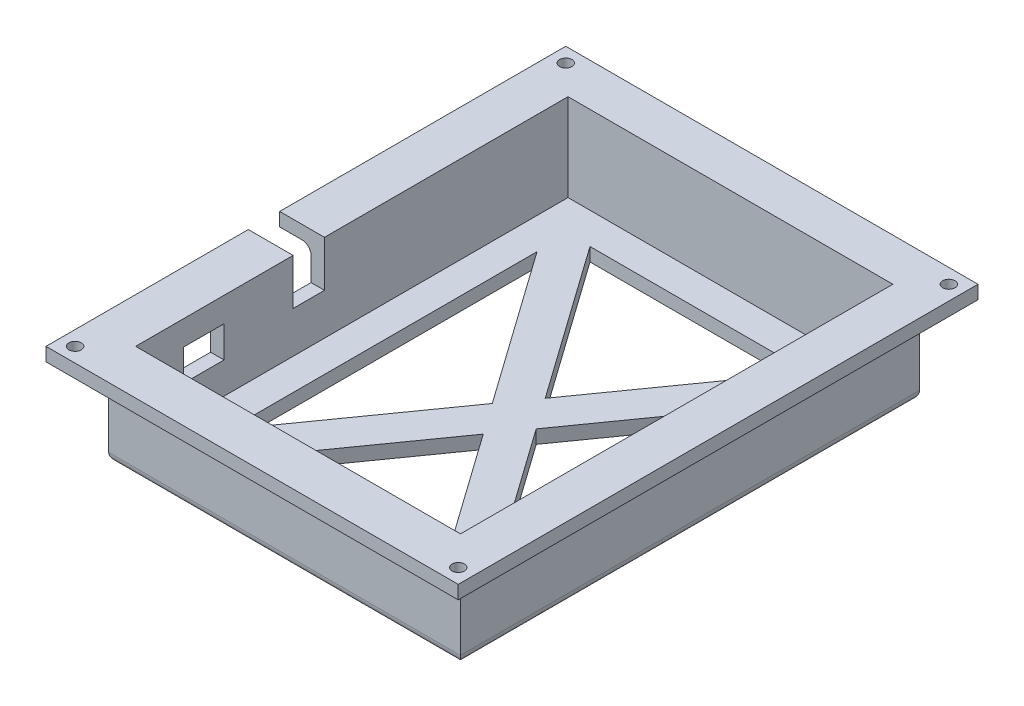
SolidWorks part; units mm, degrees
ref_plane "Front" through (0, 0, 0) normal (0, 0, 1) x (1, 0, 0)
ref_plane "Top" through (0, 0, 0) normal (0, 1, 0) x (1, 0, 0)
ref_plane "Right" through (0, 0, 0) normal (1, 0, 0) x (0, 0, -1)
sketch "Sketch1" plane through (0, 0, 0) normal (0, 1, 0) x (1, 0, 0)
  line L1 (0, 0) -> (72.5, 0)
  line L2 (0, 0) -> (0, 96.5)
  line L3 (0, 96.5) -> (72.5, 96.5)
  line L4 (72.5, 0) -> (72.5, 96.5)
  dimension "D1" = 96.5
  dimension "D2" = 72.5
extrude "bracketBase" add sketch "Sketch1" along normal blind 3
sketch "Sketch3" plane through (0, 0, 0) normal (0, -1, 0) x (1, 0, 0)
  line L0 (-3, 3) -> (-3, -99.5)
  line L1 (-3, -99.5) -> (75.5, -99.5)
  line L2 (75.5, -99.5) -> (75.5, 3)
  line L3 (75.5, 3) -> (-3, 3)
  line L4 (0, 0) -> (0, -96.5)
  line L5 (0, -96.5) -> (72.5, -96.5)
  line L6 (72.5, -96.5) -> (72.5, 0)
  line L7 (72.5, 0) -> (0, 0)
  line L8 (0, 0) -> (0, -96.5)
  line L9 (0, -96.5) -> (72.5, -96.5)
  line L10 (72.5, -96.5) -> (72.5, 0)
  line L11 (72.5, 0) -> (0, 0)
  dimension "D1" = 0
  dimension "D2" = 3
extrude "bracketWalls" add sketch "Sketch3" against normal blind 22.5
sketch "Sketch4" plane through (72.5, 0, 0) normal (-1, 0, 0) x (0, 0, 1)
  line L0 (0, 3) -> (-96.5, 3) construction
  line L1 (-42.15, 3) -> (-35.15, 3)
  line L2 (-42.15, 3) -> (-42.15, 22.5)
  line L3 (-42.15, 22.5) -> (-35.15, 22.5)
  line L4 (-35.15, 3) -> (-35.15, 22.5)
  line L5 (-96.5, 22.5) -> (0, 22.5) construction
  line L6 (0, 22.5) -> (0, 3) construction
  dimension "D1" = 42.15
  dimension "D2" = 7
extrude "wireHole" cut sketch "Sketch4" against normal blind 22.5
sketch "Sketch6" plane through (0, 22.5, 0) normal (0, 1, 0) x (1, 0, 0)
  line L12 (72.5, 96.5) -> (72.5, 42.15)
  line L13 (72.5, 42.15) -> (75.5, 42.15)
  line L14 (75.5, 42.15) -> (75.5, 99.5)
  line L15 (75.5, 99.5) -> (-3, 99.5)
  line L16 (-3, 99.5) -> (-3, -3)
  line L17 (-3, -3) -> (75.5, -3)
  line L18 (75.5, -3) -> (75.5, 35.15)
  line L19 (75.5, 35.15) -> (72.5, 35.15)
  line L20 (72.5, 35.15) -> (72.5, 0)
  line L21 (72.5, 0) -> (0, 0)
  line L22 (0, 0) -> (0, 96.5)
  line L23 (0, 96.5) -> (72.5, 96.5)
  line L24 (72.5, 96.5) -> (72.5, 42.15)
  line L32 (72.5, 35.15) -> (72.5, 0)
  line L33 (72.5, 0) -> (0, 0)
  line L34 (0, 0) -> (0, 96.5)
  line L35 (0, 96.5) -> (72.5, 96.5)
  line L48 (82, 42.15) -> (82, 106)
  line L49 (82, 106) -> (-10, 106)
  line L50 (-10, 106) -> (-10, -10)
  line L51 (-10, -10) -> (82, -10)
  line L52 (82, -10) -> (82, 35.15)
  line L53 (72.5, 35.15) -> (82, 35.15)
  line L54 (72.5, 42.15) -> (82, 42.15)
  dimension "D1" = 0
extrude "bracketFlange" add sketch "Sketch6" against normal blind 3
sketch "Sketch7" plane through (0, 19.5, 0) normal (0, -1, 0) x (1, 0, 0)
  line L0 (-10, -48) -> (82, -48) construction
  line L1 (-10, -106) -> (-10, 10) construction
  line L2 (75.5, -99.5) -> (82, -106) construction
  line L3 (82, -42.15) -> (82, -106) construction
  line L4 (36, -106) -> (36, 10) construction
  line L5 (82, -106) -> (-10, -106) construction
  line L6 (-10, 10) -> (82, 10) construction
  circle A0 centre (78.75, -102.75) radius 1.375
  circle A1 centre (78.75, 6.75) radius 1.375
  circle A2 centre (-6.75, -102.75) radius 1.375
  circle A3 centre (-6.75, 6.75) radius 1.375
  dimension "D1" = 2.75
extrude "mountingHoles" cut sketch "Sketch7" against normal through all
ref_plane "Plane1" through (36, 0, 0) normal (1, 0, 0) x (0, 0, -1)
mirror "Mirror1" about plane through (36, 0, 0) normal (1, 0, 0) of "wireHole"
sketch "Sketch8" plane through (-3, 0, 0) normal (-1, 0, 0) x (0, 0, 1)
  line L0 (-10.73, 17) -> (-10.73, 10)
  line L1 (-35.15, 19.5) -> (-35.15, 3) construction
  line L2 (-19.73, 10) -> (-19.73, 17)
  line L3 (-19.73, 10) -> (-10.73, 10)
  line L4 (-10.73, 17) -> (-19.73, 17)
  line L5 (-35.15, 22.5) -> (10, 22.5) construction
  dimension "D1" = 9
  dimension "D2" = 15.42
  dimension "D3" = 7
  dimension "D4" = 5.5
extrude "switchHole" cut sketch "Sketch8" against normal blind 10
sketch "Sketch9" plane through (0, 0, -35.15) normal (0, 0, -1) x (-1, 0, 0)
  line L6 (-72.5, 3) -> (-72.5, 22.5)
  line L7 (-72.5, 22.5) -> (-82, 22.5)
  line L8 (-82, 22.5) -> (-82, 19.5)
  line L9 (-82, 19.5) -> (-75.5, 19.5)
  line L10 (-75.5, 19.5) -> (-75.5, 3)
  line L11 (-75.5, 3) -> (-72.5, 3)
  line L12 (-72.5, 3) -> (-72.5, 22.5)
  line L13 (-72.5, 22.5) -> (-82, 22.5)
  line L14 (-82, 22.5) -> (-82, 19.5)
  line L15 (-82, 19.5) -> (-75.5, 19.5)
  line L16 (-75.5, 19.5) -> (-75.5, 3)
  line L17 (-75.5, 3) -> (-72.5, 3)
  dimension "D1" = 0
extrude "Boss-Extrude1" add sketch "Sketch9" along normal up to next
sketch "Sketch10" plane through (0, 0, 0) normal (0, -1, 0) x (1, 0, 0)
  line L4 (-0.5, -35.15) -> (-3, -35.15)
  line L5 (-0.5, -42.15) -> (-0.5, -35.15)
  line L6 (-3, -42.15) -> (-0.5, -42.15)
  line L7 (-3, -35.15) -> (-3, -42.15)
  line L8 (-0.5, -35.15) -> (-3, -35.15)
  line L9 (-0.5, -42.15) -> (-0.5, -35.15)
  line L10 (-3, -42.15) -> (-0.5, -42.15)
  line L11 (-3, -35.15) -> (-3, -42.15)
  dimension "D1" = 0
extrude "Boss-Extrude2" add sketch "Sketch10" against normal blind 12.25
fillet "Fillet1" radius 2 5 edges at (-3, 19.5, -70.825) (36.25, 19.5, -99.5) (75.5, 19.5, -48.25) (36.25, 19.5, 3) (-3, 19.5, -16.075)
fillet "Fillet2" radius 2 4 edges at (36.25, 0, 3) (75.5, 0, -48.25) (36.25, 0, -99.5) (-3, 0, -48.25)
sketch "Sketch11" plane through (-0.5, 0, 0) normal (-1, 0, 0) x (0, 0, 1)
  line L4 (-42.15, 22.5) -> (-42.15, 12.25)
  line L5 (-42.15, 12.25) -> (-35.15, 12.25)
  line L6 (-35.15, 12.25) -> (-35.15, 22.5)
  line L7 (-35.15, 22.5) -> (-42.15, 22.5)
  line L8 (-42.15, 22.5) -> (-42.15, 12.25)
  line L9 (-42.15, 12.25) -> (-35.15, 12.25)
  line L10 (-35.15, 12.25) -> (-35.15, 22.5)
  line L11 (-35.15, 22.5) -> (-42.15, 22.5)
  dimension "D1" = 0
extrude "Cut-Extrude1" cut sketch "Sketch11" against normal blind 10
sketch "Sketch12" plane through (0, 0, 0) normal (0, -1, 0) x (1, 0, 0)
  line L4 (7, -89.5) -> (65.5, -7) construction
  line L5 (65.5, -89.5) -> (7, -7) construction
  line L6 (11.9036, -89.5) -> (36.25, -55.1653)
  line L7 (65.5, -82.5847) -> (41.1536, -48.25)
  line L8 (65.5, -89.5) -> (65.5, -7)
  line L9 (65.5, -7) -> (7, -7)
  line L10 (7, -7) -> (7, -89.5)
  line L11 (7, -89.5) -> (65.5, -89.5)
  line L12 (65.5, -82.5847) -> (65.5, -13.9153)
  line L13 (60.5964, -7) -> (11.9036, -7)
  line L14 (7, -13.9153) -> (7, -82.5847)
  line L15 (11.9036, -89.5) -> (60.5964, -89.5)
  line L16 (7, -82.5847) -> (31.3464, -48.25)
  line L17 (60.5964, -89.5) -> (36.25, -55.1653)
  line L18 (3.7371, -87.1863) -> (62.2371, -4.6863) construction
  line L19 (10.2629, -91.8137) -> (68.7629, -9.3137) construction
  line L20 (62.2371, -91.8137) -> (3.7371, -9.3137) construction
  line L21 (68.7629, -87.1863) -> (10.2629, -4.6863) construction
  line L22 (31.3464, -48.25) -> (7, -13.9153)
  line L23 (41.1536, -48.25) -> (65.5, -13.9153)
  line L24 (36.25, -41.3347) -> (60.5964, -7)
  line L25 (36.25, -41.3347) -> (11.9036, -7)
  dimension "D1" = 8
  dimension "D2" = 4
  dimension "D3" = 4
extrude "weightReduction1" cut sketch "Sketch12" against normal through all
